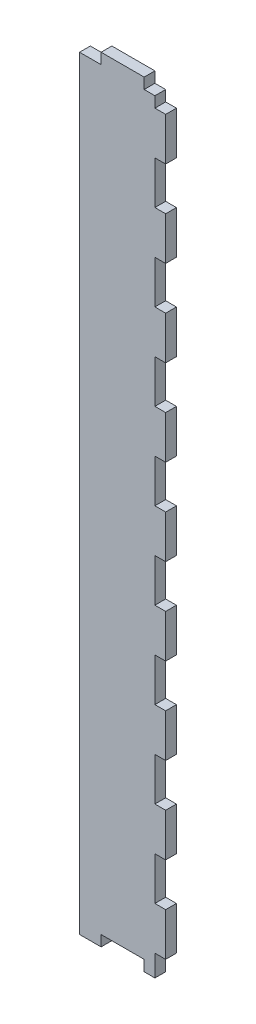
SolidWorks part; units mm, degrees
ref_plane "Front Plane" through (0, 0, 0) normal (0, 0, 1) x (1, 0, 0)
ref_plane "Top Plane" through (0, 0, 0) normal (0, 1, 0) x (1, 0, 0)
ref_plane "Right Plane" through (0, 0, 0) normal (1, 0, 0) x (0, 0, -1)
sketch "Sketch1" plane through (0, 0, 0) normal (0, 0, 1) x (1, 0, 0)
  line L1 (0, 0) -> (25.4, 0)
  line L2 (0, 0) -> (0, 228.6)
  line L3 (0, 228.6) -> (25.4, 228.6)
  line L4 (25.4, 0) -> (25.4, 228.6)
  dimension "D1" = 228.6
  dimension "D2" = 25.4
extrude "Extrude1" add sketch "Sketch1" along normal blind 3.175
sketch "Sketch3" plane through (0, 0, 3.175) normal (0, 0, 1) x (1, 0, 0)
  line L0 (25.4, 0) -> (25.4, 228.6) construction
  line L1 (25.4, 222.25) -> (22.225, 222.25)
  line L2 (25.4, 222.25) -> (25.4, 228.6)
  line L3 (25.4, 228.6) -> (22.225, 228.6)
  line L4 (22.225, 222.25) -> (22.225, 228.6)
  dimension "D1" = 6.35
  dimension "D2" = 3.175
  dimension "D3" = 6.35
extrude "Cut-Extrude1" cut sketch "Sketch3" against normal blind 3.175
pattern_linear "LPattern1" count 2 spacing 222.25 along (0, -1, 0) of "Cut-Extrude1"
sketch "Sketch4" plane through (0, 0, 3.175) normal (0, 0, 1) x (1, 0, 0)
  line L0 (25.4, 6.35) -> (25.4, 222.25) construction
  line L1 (25.4, 209.55) -> (22.225, 209.55)
  line L2 (25.4, 209.55) -> (25.4, 196.85)
  line L3 (25.4, 196.85) -> (22.225, 196.85)
  line L4 (22.225, 209.55) -> (22.225, 196.85)
  line L5 (22.225, 228.6) -> (0, 228.6) construction
  dimension "D1" = 12.7
  dimension "D2" = 3.175
  dimension "D3" = 19.05
extrude "Cut-Extrude2" cut sketch "Sketch4" against normal blind 3.175
pattern_linear "LPattern2" count 8 spacing 25.4 along (0, -1, 0) of "Cut-Extrude2"
sketch "Sketch5" plane through (0, 0, 3.175) normal (0, 0, 1) x (1, 0, 0)
  line L0 (0, 0) -> (22.225, 0) construction
  line L1 (19.05, 0) -> (6.35, 0)
  line L2 (19.05, 0) -> (19.05, 3.175)
  line L3 (19.05, 3.175) -> (6.35, 3.175)
  line L4 (6.35, 0) -> (6.35, 3.175)
  dimension "D1" = 6.35
  dimension "D2" = 12.7
  dimension "D3" = 3.175
extrude "Cut-Extrude3" cut sketch "Sketch5" against normal blind 3.175
sketch "Sketch6" plane through (0, 0, 3.175) normal (0, 0, 1) x (1, 0, 0)
  line L1 (0, 228.6) -> (6.35, 228.6)
  line L2 (0, 228.6) -> (0, 225.425)
  line L3 (0, 225.425) -> (6.35, 225.425)
  line L4 (6.35, 228.6) -> (6.35, 225.425)
  dimension "D1" = 6.35
  dimension "D2" = 3.175
extrude "Cut-Extrude4" cut sketch "Sketch6" against normal blind 3.175
pattern_linear "LPattern3" count 2 spacing 19.05 along (1, 0, 0) of "Cut-Extrude4"
